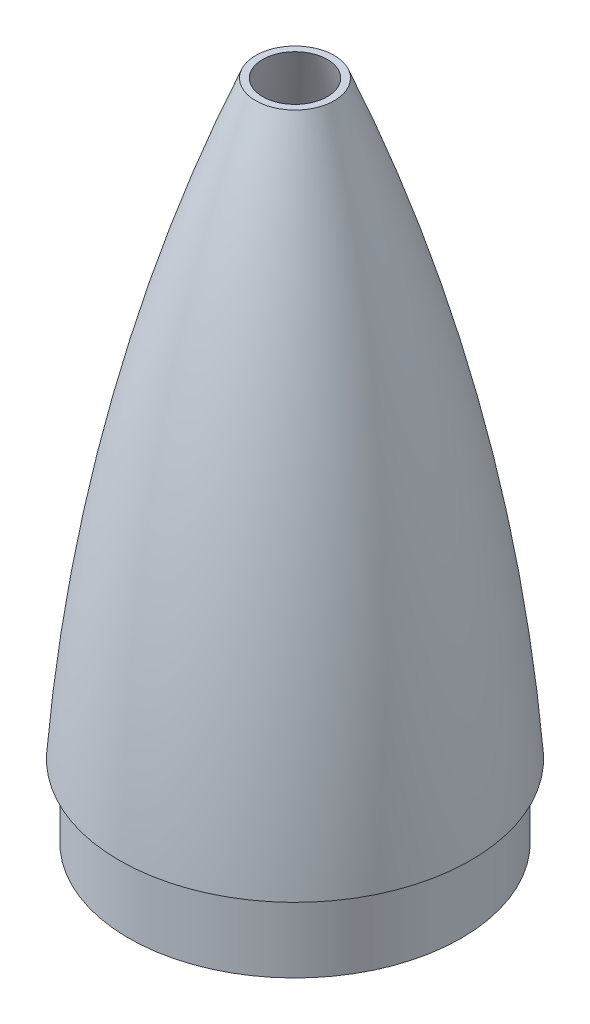
SolidWorks part; units mm, degrees
material "PVB"
ref_plane "Front Plane" through (0, 0, 0) normal (0, 0, 1) x (1, 0, 0)
ref_plane "Top Plane" through (0, 0, 0) normal (0, 1, 0) x (1, 0, 0)
ref_plane "Right Plane" through (0, 0, 0) normal (1, 0, 0) x (0, 0, -1)
sketch "Sketch2" plane through (0, 0, 0) normal (0, 0, 1) x (1, 0, 0)
  line L0 (0, 0) -> (0, 381) construction
  line L1 (-98.425, 0) -> (-90.551, 0)
  line L2 (0, 381) -> (0, 375.92)
  arc A0 (0, 381) -> (-98.425, 0) centre (992.1135, -78.5092) ccw
  arc A1 (0, 375.92) -> (-90.551, 0) centre (1112.691, -90.9691) ccw
  dimension "D1" = 381
  dimension "D2" = 5.08
  dimension "D3" = 98.425
  dimension "D4" = 7.874
revolve "Revolve1" add sketch "Sketch2" angle 360 about L2
sketch "Sketch3" plane through (0, 0, 0) normal (0, -1, 0) x (1, 0, 0)
  circle A0 centre (0, 0) radius 88.9
  circle A1 centre (0, 0) radius 86.995
  dimension "D1" = 177.8
extrude "Boss-Extrude1" [suppressed] add sketch "Sketch3" along normal blind 35.56
sketch "Sketch4" plane through (0, 0, 0) normal (0, -1, 0) x (-1, 0, 0)
  circle A0 centre (0, 0) radius 93.1545
  circle A1 centre (0, 0) radius 90.4875
  dimension "D1" = 186.309
  dimension "D2" = 180.975
extrude "Boss-Extrude2" add sketch "Sketch4" along normal blind 40.4
ref_plane "Plane1" through (0, -17.54, 0) normal (0, -1, 0) x (-1, 0, 0)
sketch "Sketch6" plane through (0, -17.54, 0) normal (0, -1, 0) x (-1, 0, 0)
  circle A0 centre (0, 0) radius 221.0288
extrude "Cut-Extrude1" [suppressed] cut sketch "Sketch6" against normal blind 457.2
ref_plane "Plane2" through (0, 381, 0) normal (0, 1, 0) x (1, 0, 0)
sketch "Sketch7" plane through (0, 381, 0) normal (0, 1, 0) x (1, 0, 0)
  circle A0 centre (0, 0) radius 317.5
  dimension "D1" = 635
extrude "Cut-Extrude2" cut sketch "Sketch7" against normal blind 50.8
